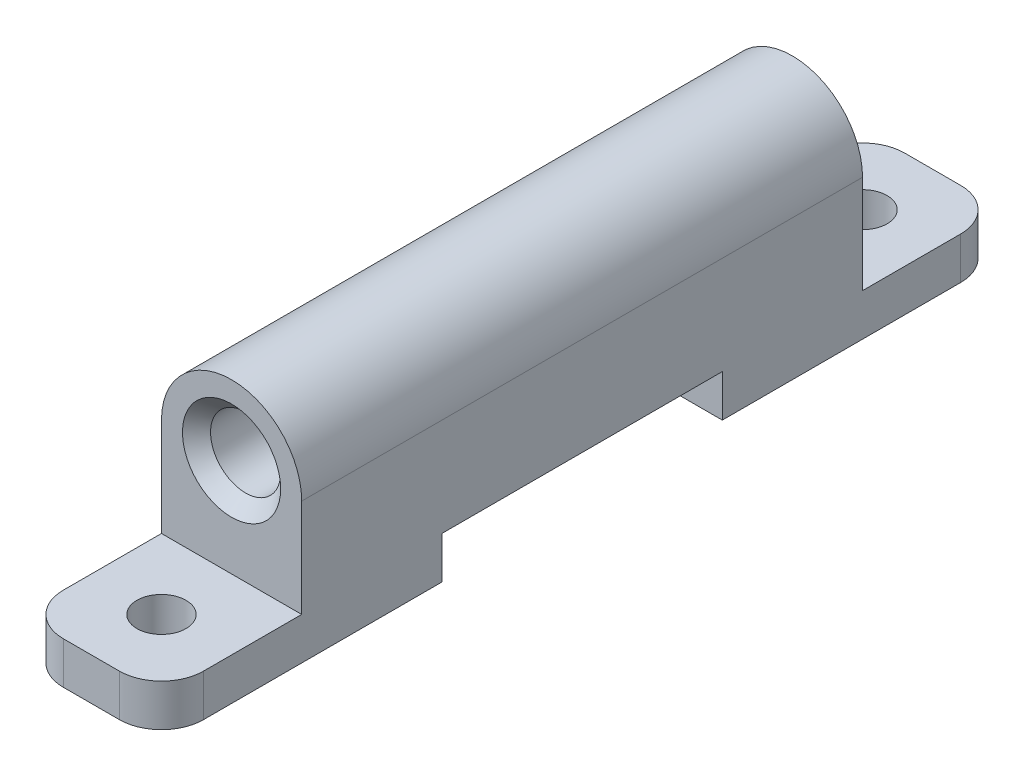
SolidWorks part; units mm, degrees
ref_plane "正面(Front)" through (0, 0, 0) normal (0, 0, 1) x (1, 0, 0)
ref_plane "平面(Top)" through (0, 0, 0) normal (0, 1, 0) x (1, 0, 0)
ref_plane "右側面(Right)" through (0, 0, 0) normal (1, 0, 0) x (0, 0, -1)
sketch "ｽｹｯﾁ1" plane through (0, 0, 0) normal (0, 0, 1) x (1, 0, 0)
  line L0 (0, 0) -> (0, 16.6588) construction
  line L1 (-5, 0) -> (5, 0)
  line L2 (5, 0) -> (5, 7)
  line L3 (-5, 0) -> (-5, 7)
  arc A0 (5, 7) -> (-5, 7) centre (0, 7) ccw
  circle A1 centre (0, 7) radius 2.5
  dimension "D3" = 5
  dimension "D1" = 10
  dimension "D2" = 7
extrude "ﾎﾞｽ - 押し出し1" add sketch "ｽｹｯﾁ1" along normal mid plane 40
sketch "ｽｹｯﾁ2" plane through (0, 0, 0) normal (0, -1, 0) x (1, 0, 0)
  line L0 (-5, 20) -> (-5, -20) construction
  line L1 (-5, 10) -> (5, 10)
  line L2 (-5, 10) -> (-5, 30)
  line L3 (-5, 30) -> (5, 30)
  line L4 (5, 10) -> (5, 30)
  line L5 (5, 20) -> (5, -20) construction
  line L6 (-5, 20) -> (5, 20) construction
  dimension "D1" = 10
  dimension "D2" = 10
extrude "ﾎﾞｽ - 押し出し2" add sketch "ｽｹｯﾁ2" along normal blind 3
sketch "ｽｹｯﾁ3" plane through (0, 0, 0) normal (0, 1, 0) x (1, 0, 0)
  line L0 (5, -20) -> (5, -30) construction
  line L1 (5, -30) -> (-5, -30) construction
  circle A0 centre (0, -25) radius 1.75
  dimension "D1" = 3.5
  dimension "D2" = 5
  dimension "D3" = 5
extrude "ｶｯﾄ - 押し出し1" cut sketch "ｽｹｯﾁ3" against normal through all
fillet "ﾌｨﾚｯﾄ1" radius 3 2 edges at (-5, -1.5, 30) (5, -1.5, 30)
mirror "ﾐﾗｰ1" about plane through (0, 0, 0) normal (0, 0, 1) of "ﾌｨﾚｯﾄ1", "ｶｯﾄ - 押し出し1", "ﾎﾞｽ - 押し出し2"
chamfer "面取り1" distance 1 angle 45 2 edges at (2.5, 7, -20) (2.5, 7, 20)
